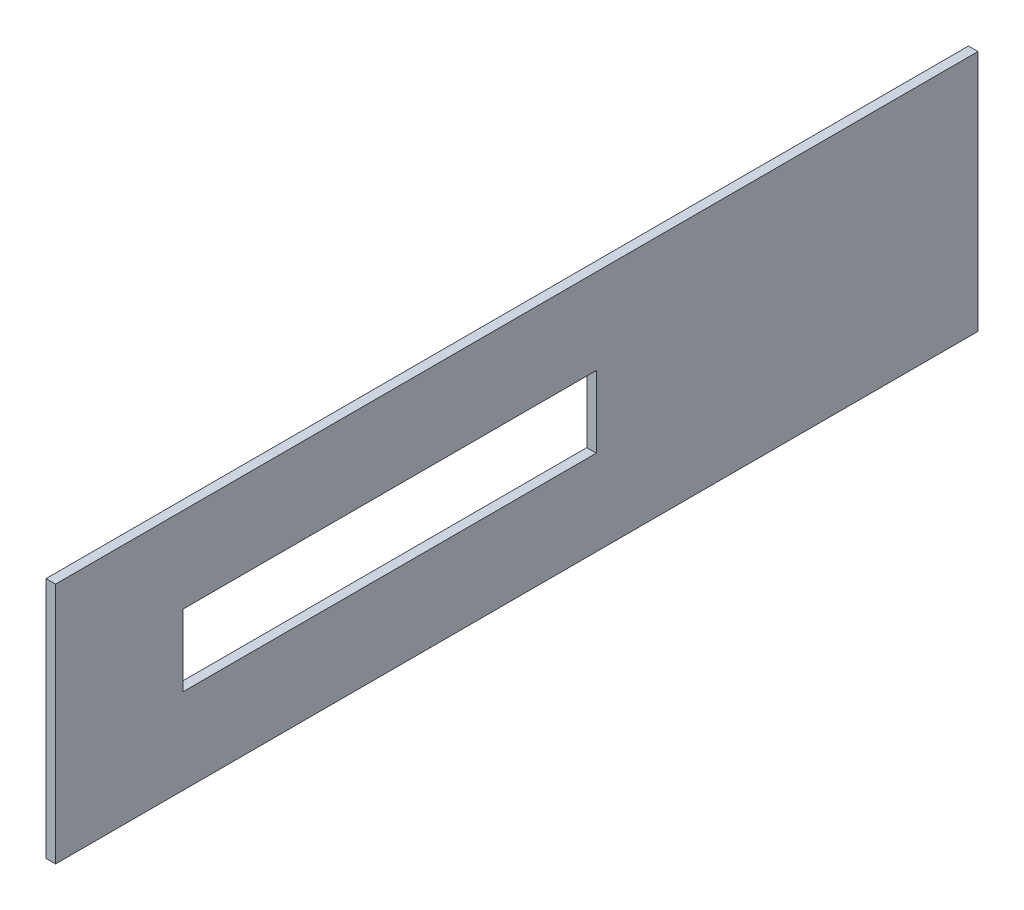
SolidWorks part; units mm, degrees
ref_plane "Front Plane" through (0, 0, 0) normal (0, 0, 1) x (1, 0, 0)
ref_plane "Top Plane" through (0, 0, 0) normal (0, 1, 0) x (1, 0, 0)
ref_plane "Right Plane" through (0, 0, 0) normal (1, 0, 0) x (0, 0, -1)
sketch "Sketch1" plane through (0, 0, 0) normal (1, 0, 0) x (0, 0, -1)
  line L1 (-145, -38.1) -> (145, -38.1)
  line L2 (-145, -38.1) -> (-145, 38.1)
  line L3 (-145, 38.1) -> (145, 38.1)
  line L4 (145, -38.1) -> (145, 38.1)
  line L5 (-145, -38.1) -> (145, 38.1) construction
  line L6 (-145, 38.1) -> (145, -38.1) construction
  point P0 (0, 0)
  dimension "D1" = 76.2
  dimension "D2" = 290
extrude "Boss-Extrude1" add sketch "Sketch1" along normal blind 3
sketch "Sketch2" plane through (3, 0, 0) normal (1, 0, 0) x (0, 0, -1)
  line L0 (25, -11.25) -> (25, 11.25)
  line L5 (25, 11.25) -> (-105, 11.25)
  line L6 (-105, 11.25) -> (-105, -11.25)
  line L7 (-105, -11.25) -> (25, -11.25)
  line L8 (-145, 38.1) -> (-145, -38.1) construction
  line L9 (0, 0) -> (25, 0) construction
  point P9 (25.1404, -11.25)
  dimension "D1" = 22.5
  dimension "D2" = 40
  dimension "D3" = 130
extrude "Cut-Extrude1" cut sketch "Sketch2" against normal through all
